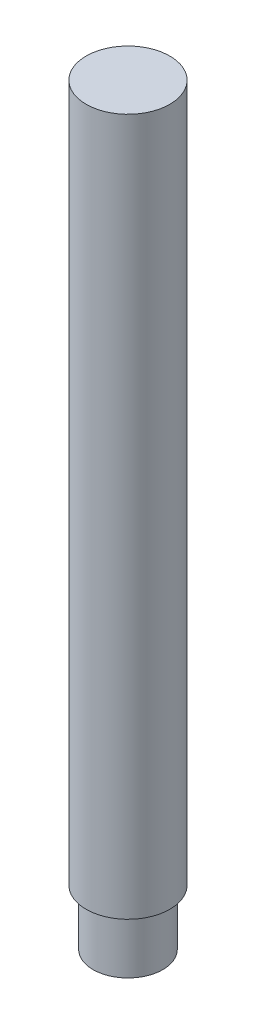
SolidWorks part; units mm, degrees
ref_plane "Front Plane" through (0, 0, 0) normal (0, 0, 1) x (1, 0, 0)
ref_plane "Top Plane" through (0, 0, 0) normal (0, 1, 0) x (1, 0, 0)
ref_plane "Right Plane" through (0, 0, 0) normal (1, 0, 0) x (0, 0, -1)
sketch "Sketch1" plane through (0, 0, 0) normal (0, 0, 1) x (1, 0, 0)
  line L0 (0, 48.8954) -> (0, -45.4178) construction
  line L1 (0, 54) -> (3, 54)
  line L2 (3, 54) -> (3, 4)
  line L3 (3, 4) -> (2.5, 4)
  line L4 (2.5, 4) -> (2.5, 0)
  line L5 (2.5, 0) -> (0, 0)
  line L6 (0, 0) -> (0, 54)
  line L7 (55, 0) -> (-55, 0) construction
  dimension "D1" = 2.5
  dimension "D2" = 3
  dimension "D3" = 4
  dimension "D4" = 50
revolve "Revolve1" add sketch "Sketch1" angle 360 about L0
